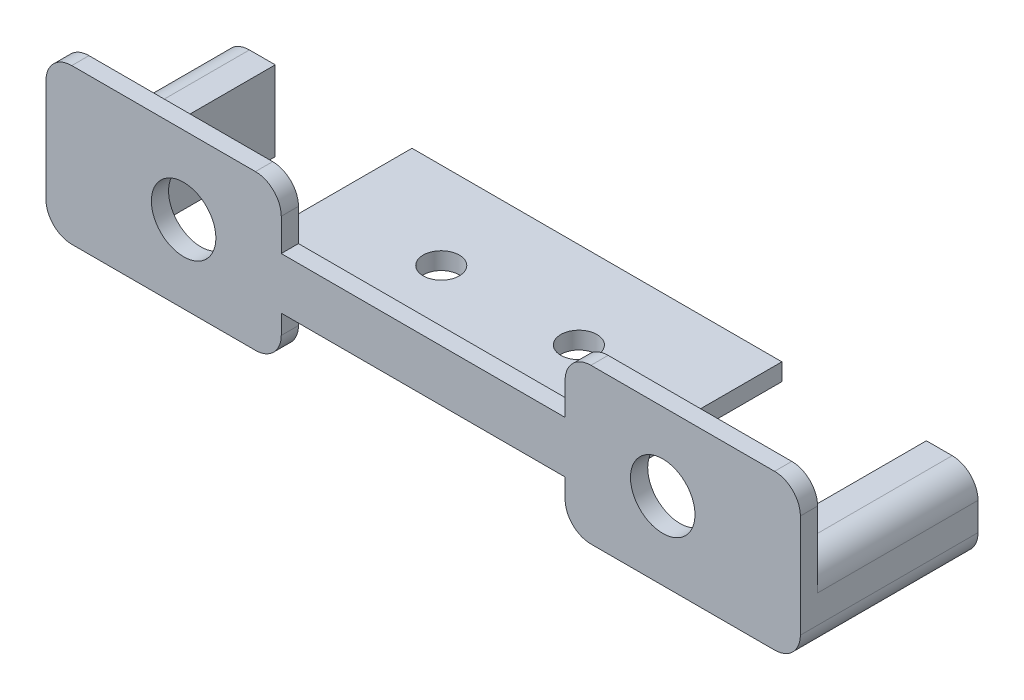
SolidWorks part; units mm, degrees
ref_plane "Front Plane" through (0, 0, 0) normal (0, 0, 1) x (1, 0, 0)
ref_plane "Top Plane" through (0, 0, 0) normal (0, 1, 0) x (1, 0, 0)
ref_plane "Right Plane" through (0, 0, 0) normal (1, 0, 0) x (0, 0, -1)
sketch "Sketch3" plane through (0, 0, 0) normal (0, 1, 0) x (1, 0, 0)
  line L1 (-21.5, 0) -> (21.5, 0)
  line L2 (-21.5, 0) -> (-21.5, 18.2)
  line L3 (-21.5, 18.2) -> (21.5, 18.2)
  line L4 (21.5, 0) -> (21.5, 18.2)
  line L5 (-8, 8.1) -> (8, 8.1) construction
  circle A0 centre (-8, 8.1) radius 2.1
  circle A1 centre (8, 8.1) radius 2.1
  point P6 (0, 0)
  point P12 (0, 8.1)
  dimension "D2" = 4.2
  dimension "D1" = 16
  dimension "D3" = 8
  dimension "D4" = 6
  dimension "D5" = 43
extrude "Boss-Extrude5" add sketch "Sketch3" against normal blind 2 separate body
sketch "Sketch1" plane through (0, 0, 0) normal (0, 0, 1) x (1, 0, 0)
  line L0 (0, -1000) -> (0, 49000) construction
  line L1 (-43.85, -9.25) -> (-16.5, -9.25)
  line L2 (-43.85, -9.25) -> (-43.85, 8.75)
  line L4 (43.85, -9.25) -> (43.85, 8.75)
  line L5 (-43.85, -0.25) -> (43.85, -0.25) construction
  line L6 (-43.85, 8.75) -> (-16.5, 8.75)
  line L15 (-37.85, -24) -> (-37.85, 0) construction
  line L16 (-16.5, 8.75) -> (-16.5, 2)
  line L17 (-16.5, -9.25) -> (-16.5, -4)
  line L18 (-16.5, -4) -> (16.5, -4)
  line L19 (16.5, -4) -> (16.5, -9.25)
  line L20 (16.5, -9.25) -> (43.85, -9.25)
  line L21 (-16.5, 2) -> (16.5, 2)
  line L22 (-21.5, -2) -> (21.5, -2) construction
  line L23 (-21.5, 0) -> (21.5, 0) construction
  line L24 (-21.5, -2) -> (-21.5, 0) construction
  line L25 (16.5, 2) -> (16.5, 8.75)
  line L26 (16.5, 8.75) -> (43.85, 8.75)
  circle A0 centre (-27.85, -0.25) radius 3.75
  circle A2 centre (27.85, -0.25) radius 3.75
  point P14 (0, -4)
  point P32 (0, 2)
  dimension "D3" = 7.5
  dimension "D4" = 10
  dimension "D1" = 18
  dimension "D2" = 6
  dimension "D5" = 5
  dimension "D6" = 2
  dimension "D7" = 4
  dimension "D8" = 5
  dimension "D9" = 2
extrude "Boss-Extrude1" add sketch "Sketch1" along normal blind 2
chamfer "Chamfer1" distance 1.5 angle 45 1 edges at (0, -2, 0)
sketch "Sketch5" plane through (0, 0, 0) normal (0, 0, -1) x (-1, 0, 0)
  line L0 (43.85, -9.25) -> (16.5, -9.25) construction
  line L1 (43.85, 0) -> (37.85, 0)
  line L2 (43.85, 0) -> (43.85, -9.25)
  line L3 (43.85, -9.25) -> (37.85, -9.25)
  line L4 (37.85, 0) -> (37.85, -9.25)
  line L5 (37.85, -24) -> (37.85, 0) construction
  line L6 (37.85, 0) -> (60.85, 0) construction
extrude "Boss-Extrude4" add sketch "Sketch5" along normal up to surface (18.65 mm away)
mirror "Mirror2" about plane through (0, 0, 0) normal (1, 0, 0) of "Boss-Extrude4"
fillet "Fillet1" radius 3 10 edges at (-43.85, -9.25, -8.325) (-43.85, 8.75, 1) (-43.85, 0, -9.325) (43.85, 0, -9.325) (43.85, -9.25, -8.325) (43.85, 8.75, 1) (16.5, -9.25, 1) (16.5, 8.75, 1) (-16.5, 8.75, 1) (-16.5, -9.25, 1)
equation "\"width\"= 24"
equation "\"thk\"= 3"
equation "\"holesize\"= 4.2"
equation "\"holedistance\"= ( 20 + 12 ) / 2"
equation "\"threaded_hole\"= 3.9"
equation "\"fillet_radius\"= 2"
equation "\"ground_clearance\"= 25"
equation "\"tire_thk\"= 3"
equation "\"innerwheel_diam\" = \"wheel_diam\"-2*\"tire_thk\""
equation "\"innerwheel_thk\"= 8"
equation "\"wheel_diam\"= 2*(\"width\"/2+\"ground_clearance\")"
equation "\"coloursensor_holesize\"= 2.65"
equation "\"hole_to_edge\" = 4"
equation "\"D1@Sketch3\"=\"holedistance\""
equation "\"D2@Sketch3\"=\"holesize\""
